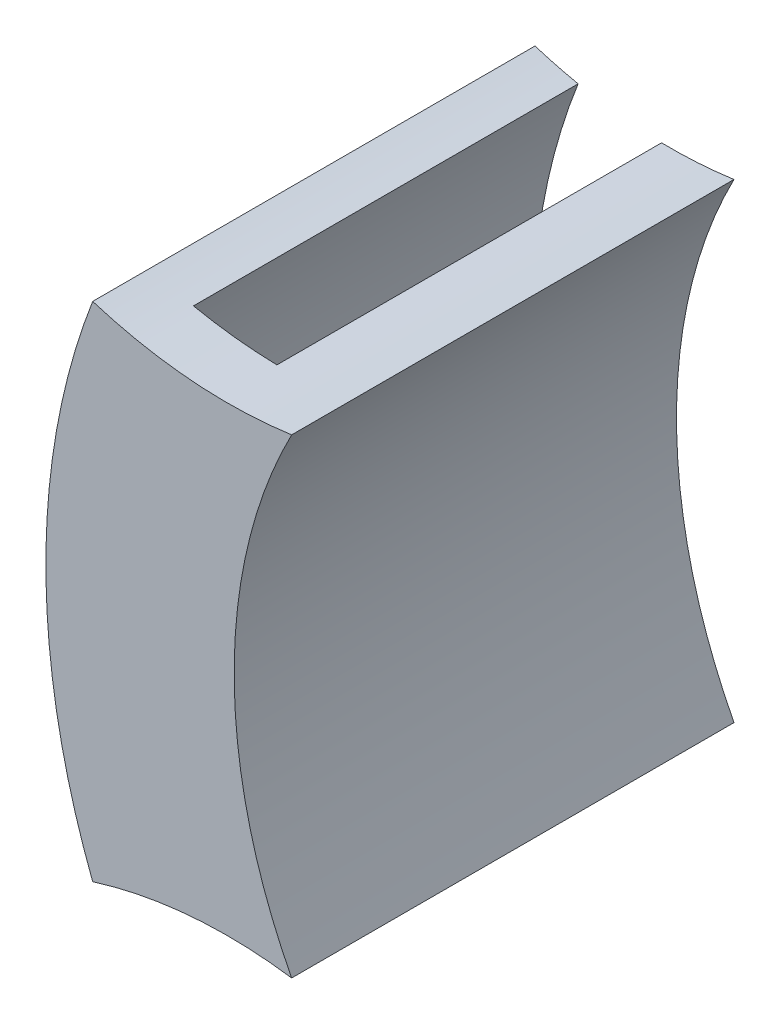
SolidWorks part; units mm, degrees
ref_plane "Front Plane" through (0, 0, 0) normal (0, 0, 1) x (1, 0, 0)
ref_plane "Top Plane" through (0, 0, 0) normal (0, 1, 0) x (1, 0, 0)
ref_plane "Right Plane" through (0, 0, 0) normal (1, 0, 0) x (0, 0, -1)
sketch "Sketch1" plane through (0, 0, 0) normal (0, 0, 1) x (1, 0, 0)
  arc A3 (28.4767, -13.0654) -> (28.4767, 13.0654) centre (62.3369, 0) cw
  arc A9 (17.0982, -20.871) -> (34.8421, -12.0019) centre (35.4954, -35.4928) ccw construction
  arc A10 (38.824, -12.2297) -> (38.824, 12.2297) centre (62.3369, 0) cw
  arc A11 (34.8421, 12.0019) -> (17.0982, 20.871) centre (35.4954, 35.4928) ccw construction
  arc A12 (38.824, 12.2297) -> (28.4767, 13.0654) centre (35.4954, 35.4928) cw
  arc A13 (28.4767, -13.0654) -> (38.824, -12.2297) centre (35.4954, -35.4928) cw
extrude "Boss-Extrude1" add sketch "Sketch1" along normal blind 3
sketch "Sketch2" plane through (0, 0, 0) normal (0, 0, -1) x (-1, 0, 0)
  arc A2 (-28.4767, -13.0654) -> (-38.824, -12.2297) centre (-35.4954, -35.4928) ccw construction
  arc A3 (-30.7185, -12.4834) -> (-30.7185, 12.4834) centre (-62.3369, 0) ccw
  arc A4 (-38.824, 12.2297) -> (-28.4767, 13.0654) centre (-35.4954, 35.4928) ccw construction
  arc A5 (-38.824, 12.2297) -> (-38.824, -12.2297) centre (-62.3369, 0) cw
  arc A6 (-35.0582, 11.9969) -> (-35.0582, -11.9969) centre (-62.3369, 0) cw
  arc A7 (-34.8421, -12.0019) -> (-17.0982, -20.871) centre (-35.4954, -35.4928) ccw construction
  arc A8 (-28.4767, 13.0654) -> (-28.4767, -13.0654) centre (-62.3369, 0) cw
  arc A9 (-20.8687, -17.0996) -> (-30.9176, -12.443) centre (-35.4954, -35.4928) ccw construction
  arc A10 (-30.7185, 12.4834) -> (-28.4767, 13.0654) centre (-35.4954, 35.4928) ccw
  arc A11 (-38.824, 12.2297) -> (-35.0582, 11.9969) centre (-35.4954, 35.4928) ccw
  arc A12 (-38.824, -12.2297) -> (-35.0582, -11.9969) centre (-35.4954, -35.4928) cw
  arc A13 (-28.4767, -13.0654) -> (-30.7185, -12.4834) centre (-35.4954, -35.4928) ccw
extrude "Boss-Extrude2" add sketch "Sketch2" along normal blind 20
